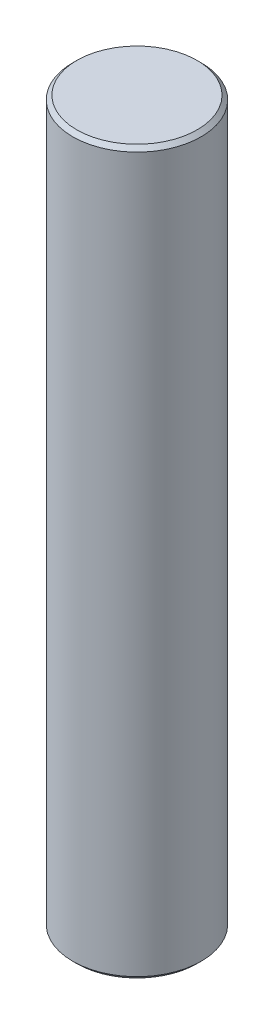
SolidWorks part; units mm, degrees
ref_plane "Front Plane" through (0, 0, 0) normal (0, 0, 1) x (1, 0, 0)
ref_plane "Top Plane" through (0, 0, 0) normal (0, 1, 0) x (1, 0, 0)
ref_plane "Right Plane" through (0, 0, 0) normal (1, 0, 0) x (0, 0, -1)
sketch "Sketch1" plane through (0, 0, 0) normal (0, 1, 0) x (1, 0, 0)
  circle A0 centre (0, 0) radius 16
  dimension "D1" = 32
extrude "Boss-Extrude1" add sketch "Sketch1" along normal blind 180
chamfer "Chamfer1" distance 1 angle 45 2 edges at (0, 0, 16) (0, 180, 16)
